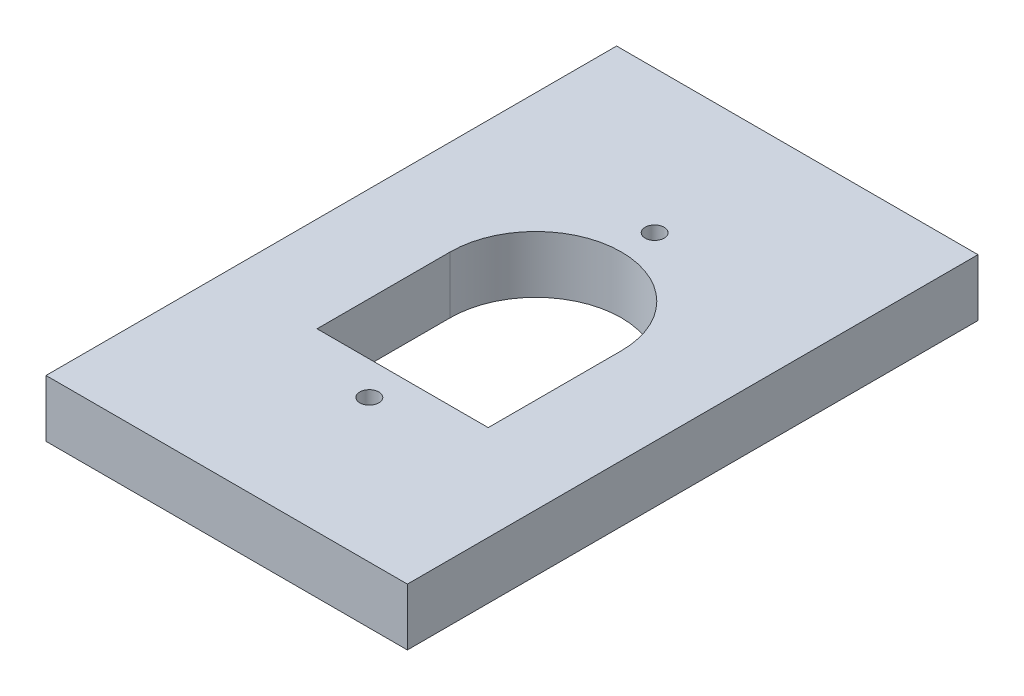
SolidWorks part; units mm, degrees
ref_plane "Front Plane" through (0, 0, 0) normal (0, 0, 1) x (1, 0, 0)
ref_plane "Top Plane" through (0, 0, 0) normal (0, 1, 0) x (1, 0, 0)
ref_plane "Right Plane" through (0, 0, 0) normal (1, 0, 0) x (0, 0, -1)
sketch "Sketch1" plane through (0, 0, 0) normal (0, 1, 0) x (1, 0, 0)
  line L1 (0, 0) -> (19, 0)
  line L2 (0, 0) -> (0, -30)
  line L3 (0, -30) -> (19, -30)
  line L4 (19, 0) -> (19, -30)
  dimension "D1" = 19
  dimension "D2" = 30
extrude "Boss-Extrude1" add sketch "Sketch1" along normal blind 3
sketch "Sketch2" plane through (0, 3, 0) normal (0, 1, 0) x (1, 0, 0)
  line L0 (9.5, 0) -> (9.5, -30) construction
  line L5 (19, 0) -> (0, 0) construction
  line L6 (0, -30) -> (19, -30) construction
  line L7 (0, -15) -> (19, -15) construction
  line L8 (0, 0) -> (0, -30) construction
  line L9 (19, -30) -> (19, 0) construction
  line B0 (9.5, -20.75) -> (9.5, -9.25) construction
  line B1 (14, -20.75) -> (14, -9.25)
  line B2 (14, -20.75) -> (5, -20.75)
  line B3 (5, -20.75) -> (5, -9.25)
  line B4 (14, -9.25) -> (5, -9.25)
  line B5 (14, -15) -> (5, -15) construction
  circle B6 centre (9.5, -13.75) radius 4.5
  circle B7 centre (9.5, -22.5) radius 0.5
  circle B8 centre (9.5, -7.5) radius 0.5
sketch_block_instance "Block1-1"
sketch_block "Block1" parameters "D3"=1, "D4"=1, "D1"=9, "D2"=11.5, "D5"=15, "D6"=7.5
extrude "Cut-Extrude1" cut sketch "Sketch2" against normal through all contours B6 B3 B2 B1 | B6 | B7 | B8
